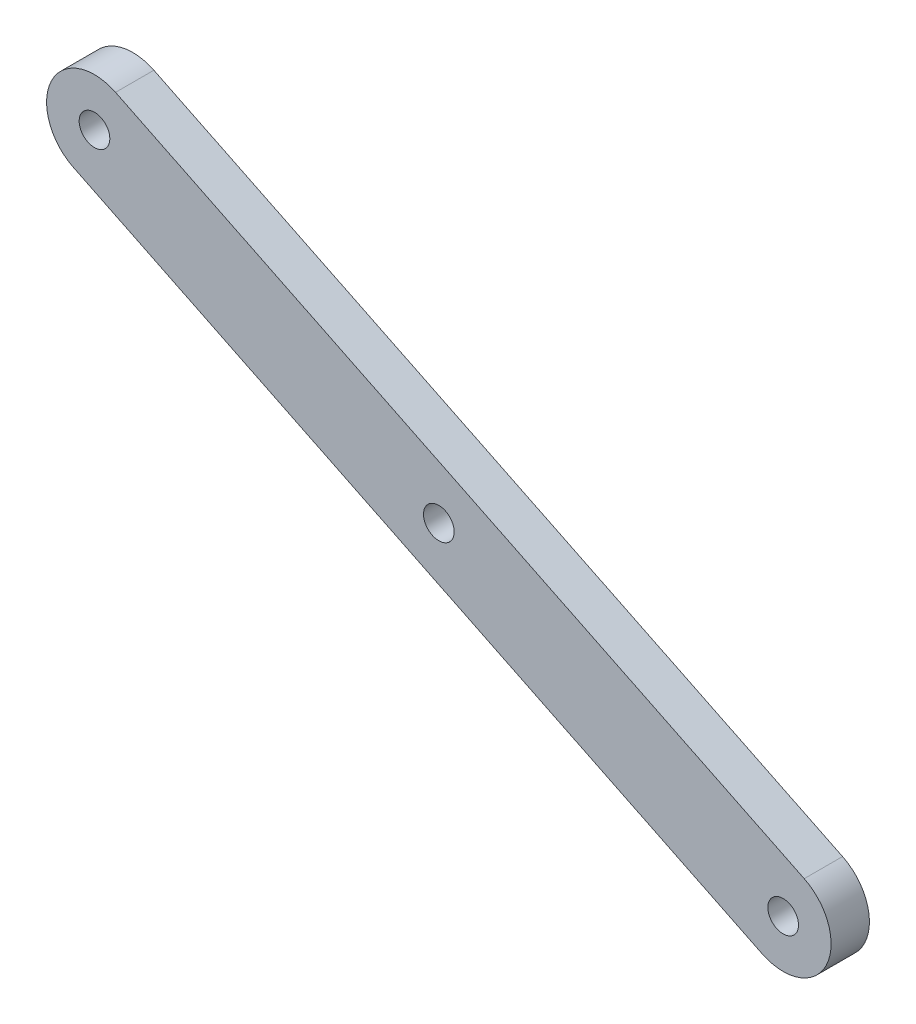
SolidWorks part; units mm, degrees
ref_plane "Front Plane" through (0, 0, 0) normal (0, 0, 1) x (1, 0, 0)
ref_plane "Top Plane" through (0, 0, 0) normal (0, 1, 0) x (1, 0, 0)
ref_plane "Right Plane" through (0, 0, 0) normal (1, 0, 0) x (0, 0, -1)
sketch "Sketch1" plane through (0, 0, 0) normal (0, 0, 1) x (1, 0, 0)
  line L0 (0, 0) -> (-71.8736, 35.131) construction
  line L1 (-2.1957, -4.4921) -> (-74.0693, 30.6389)
  line L2 (2.1957, 4.4921) -> (-69.6779, 39.6231)
  arc A0 (-2.1957, -4.4921) -> (2.1957, 4.4921) centre (0, 0) ccw
  arc A1 (-69.6779, 39.6231) -> (-74.0693, 30.6389) centre (-71.8736, 35.131) ccw
  circle A2 centre (-71.8736, 35.131) radius 1.6
  circle A3 centre (0, 0) radius 1.6
  circle A4 centre (-35.9368, 17.5655) radius 1.6
  point P3 (-35.9368, 17.5655)
  dimension "D3" = 3.2
  dimension "D1" = 10
  dimension "D2" = 80
extrude "Boss-Extrude1" add sketch "Sketch1" along normal blind 4
